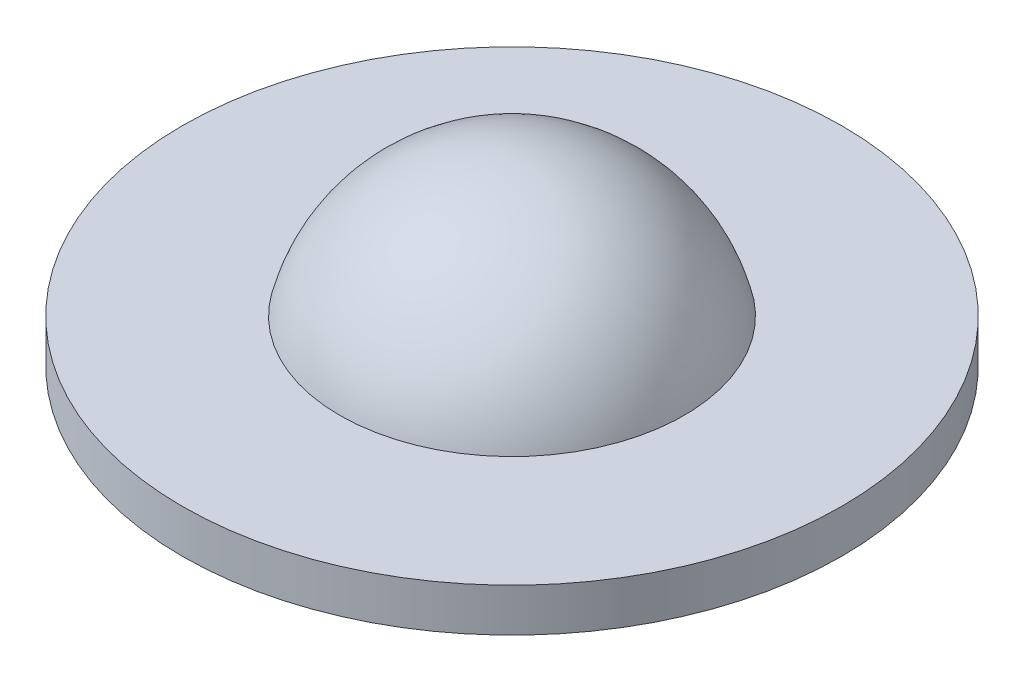
SolidWorks part; units mm, degrees
ref_plane "Front Plane" through (0, 0, 0) normal (0, 0, 1) x (1, 0, 0)
ref_plane "Top Plane" through (0, 0, 0) normal (0, 1, 0) x (1, 0, 0)
ref_plane "Right Plane" through (0, 0, 0) normal (1, 0, 0) x (0, 0, -1)
other "Bounding Box"
ref_plane "Default Plane" through (-8.9266, -12.7485, 0) normal (-0.1736, 0.9848, 0) x (0.9848, 0.1736, 0)
sketch "Sketch1" plane through (0, 0, 0) normal (1, 0, 0) x (0, 0, -1)
  line L0 (-7.9366, -0.1168) -> (-22.86, -0.1168)
  line L1 (-22.86, -0.1168) -> (-22.86, 2.8832)
  line L2 (-22.86, 2.8832) -> (-11.938, 2.8832)
  line L5 (0, 12.2812) -> (0, 0)
  line L6 (0, 0) -> (0, -7.9375)
  line L7 (0, -19.657) -> (0, -41.7062) construction
  arc A0 (-7.9366, -0.1168) -> (0, -7.9375) centre (0, 0) ccw
  arc A1 (-11.938, 2.8832) -> (0, 12.2812) centre (0, 0) cw
  point P10 (0, 3.3628)
  point P12 (-0.4018, 13.0625)
  point P13 (-7.9182, -0.5528)
  point P14 (-11.938, 8.6464)
  point P15 (0, -2.967)
  point P16 (0, -2.8314)
  point P17 (0, 0)
  dimension "D3" = 7.9375
  dimension "D1" = 11.938
  dimension "D2" = 45.72
  dimension "D4" = 9.398
  dimension "D6" = 3
revolve "Revolve1" add sketch "Sketch1" angle 360 about L7
